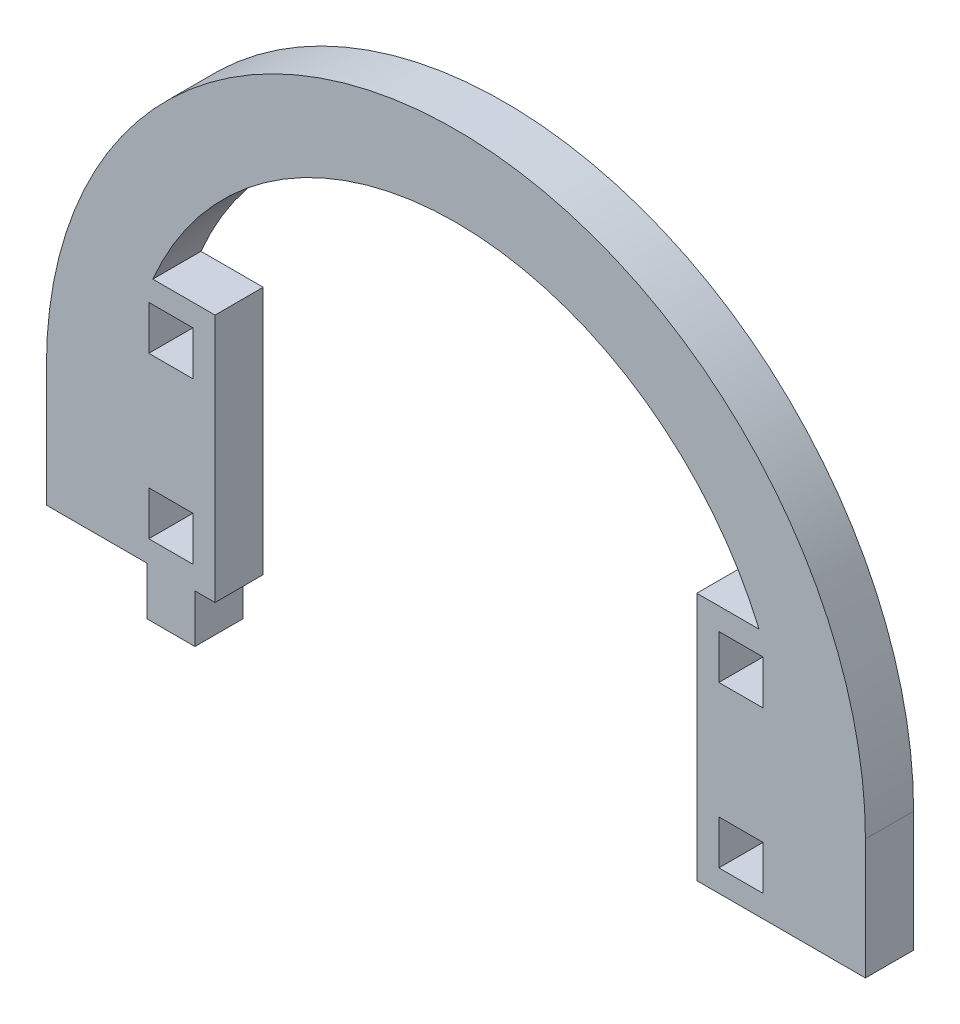
SolidWorks part; units mm, degrees
ref_plane "Front Plane" through (0, 0, 0) normal (0, 0, 1) x (1, 0, 0)
ref_plane "Top Plane" through (0, 0, 0) normal (0, 1, 0) x (1, 0, 0)
ref_plane "Right Plane" through (0, 0, 0) normal (1, 0, 0) x (0, 0, -1)
sketch "Model" plane through (0, 0, 0) normal (0, 0, 1) x (1, 0, 0)
  line L0 (3055.2252, 1463.458) -> (3055.2252, 1448.458)
  line L1 (3157.2252, 1463.458) -> (3157.2252, 1448.458)
  line L2 (3157.2252, 1448.458) -> (3147.2252, 1448.458)
  line L3 (3144.4752, 1456.708) -> (3138.9752, 1456.708)
  line L4 (3138.9752, 1456.708) -> (3138.9752, 1451.208)
  line L5 (3138.9752, 1451.208) -> (3144.4752, 1451.208)
  line L6 (3144.4752, 1451.208) -> (3144.4752, 1456.708)
  line L7 (3136.2252, 1448.458) -> (3147.2252, 1448.458)
  line L8 (3144.4752, 1476.708) -> (3138.9752, 1476.708)
  line L9 (3138.9752, 1476.708) -> (3138.9752, 1471.208)
  line L10 (3138.9752, 1471.208) -> (3144.4752, 1471.208)
  line L11 (3144.4752, 1471.208) -> (3144.4752, 1476.708)
  line L12 (3143.9743, 1479.458) -> (3136.2252, 1479.458)
  line L13 (3073.4752, 1456.708) -> (3067.9752, 1456.708)
  line L14 (3067.9752, 1456.708) -> (3067.9752, 1451.208)
  line L15 (3067.9752, 1451.208) -> (3073.4752, 1451.208)
  line L16 (3073.4752, 1451.208) -> (3073.4752, 1456.708)
  line L17 (3073.7252, 1448.458) -> (3076.2252, 1448.458)
  line L18 (3067.7252, 1448.458) -> (3067.7252, 1442.458)
  line L19 (3067.7252, 1442.458) -> (3073.7252, 1442.458)
  line L20 (3073.7252, 1442.458) -> (3073.7252, 1448.458)
  line L21 (3073.4752, 1476.708) -> (3067.9752, 1476.708)
  line L22 (3067.9752, 1476.708) -> (3067.9752, 1471.208)
  line L23 (3067.9752, 1471.208) -> (3073.4752, 1471.208)
  line L24 (3073.4752, 1471.208) -> (3073.4752, 1476.708)
  line L25 (3076.2252, 1479.458) -> (3068.476, 1479.458)
  line L26 (3076.2252, 1479.458) -> (3076.2252, 1448.458)
  line L27 (3136.2252, 1479.458) -> (3136.2252, 1448.458)
  line L28 (3055.2252, 1448.458) -> (3067.7252, 1448.458)
  arc A0 (3157.2252, 1463.458) -> (3055.2252, 1463.458) centre (3106.2252, 1463.458) ccw
  arc A1 (3143.9743, 1479.458) -> (3068.476, 1479.458) centre (3106.2252, 1463.458) ccw
extrude "Boss-Extrude1" add sketch "Model" along normal blind 6 contours L10 L11 L8 L9 | L5 L6 L3 L4 | L0 L28 L18 L19 L20 L17 L26 L25 A1 L12 L27 L7 L2 L1 A0 | L22 L23 L24 L21 | L13 L14 L15 L16
